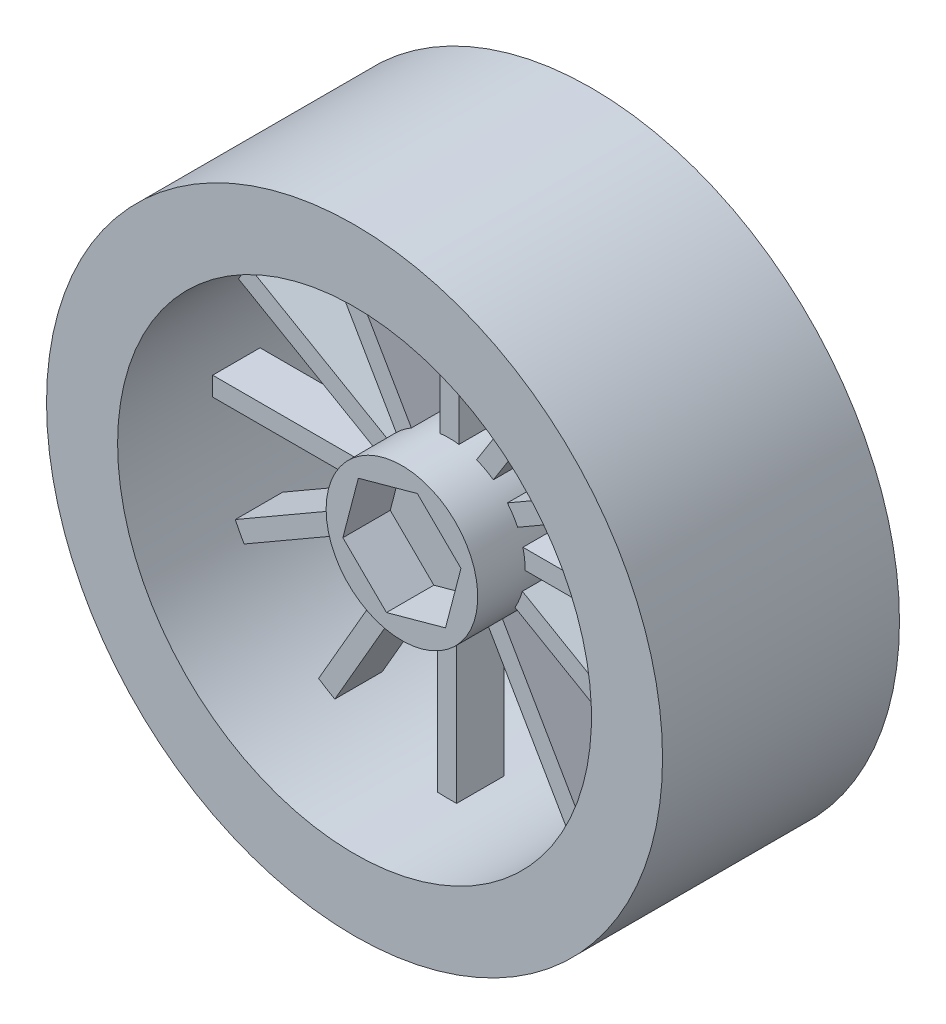
SolidWorks part; units mm, degrees
ref_plane "前视基准面" through (0, 0, 0) normal (0, 0, 1) x (1, 0, 0)
ref_plane "上视基准面" through (0, 0, 0) normal (0, 1, 0) x (1, 0, 0)
ref_plane "右视基准面" through (0, 0, 0) normal (1, 0, 0) x (0, 0, -1)
sketch "草图1" plane through (0, 0, 0) normal (0, 0, 1) x (1, 0, 0)
  circle A0 centre (0, 0) radius 32.5
extrude "凸台-拉伸1" add sketch "草图1" along normal blind 25
sketch "草图2" plane through (0, 0, 0) normal (0, 0, -1) x (-1, 0, 0)
  circle A0 centre (0, 0) radius 25
extrude "切除-拉伸1" cut sketch "草图2" against normal blind 25
sketch "草图6" plane through (0, 0, 0) normal (0, 0, -1) x (-1, 0, 0)
  circle A0 centre (0, 0) radius 8
extrude "凸台-拉伸3" add sketch "草图6" against normal blind 20 separate body contours A0
sketch "草图7" plane through (0, 0, 0) normal (0, 0, -1) x (-1, 0, 0)
  circle A0 centre (0, 0) radius 8
extrude "切除-拉伸2" cut sketch "草图7" against normal blind 5
sketch "草图8" plane through (0, 0, 5) normal (0, 0, -1) x (-1, 0, 0)
  line L1 (6.2049, 0) -> (3.1024, 5.3736)
  line L2 (3.1024, 5.3736) -> (-3.1024, 5.3736)
  line L3 (-3.1024, 5.3736) -> (-6.2049, 0)
  line L4 (-6.2049, 0) -> (-3.1024, -5.3736)
  line L5 (-3.1024, -5.3736) -> (3.1024, -5.3736)
  line L6 (3.1024, -5.3736) -> (6.2049, 0)
  circle A0 centre (0, 0) radius 5.3736 construction
extrude "切除-拉伸3" cut sketch "草图8" against normal blind 5
sketch "草图9" plane through (0, 0, 20) normal (0, 0, 1) x (1, 0, 0)
  line L1 (-1.6308, -6.2524) -> (4.5993, -4.5385)
  line L2 (4.5993, -4.5385) -> (6.2301, 1.7139)
  line L3 (6.2301, 1.7139) -> (1.6308, 6.2524)
  line L4 (1.6308, 6.2524) -> (-4.5993, 4.5385)
  line L5 (-4.5993, 4.5385) -> (-6.2301, -1.7139)
  line L6 (-6.2301, -1.7139) -> (-1.6308, -6.2524)
  circle A0 centre (0, 0) radius 5.5959 construction
extrude "切除-拉伸4" cut sketch "草图9" against normal blind 5
sketch "草图11" plane through (0, -0.7321, 10) normal (0, 0, -1) x (-1, 0, 0)
  line L0 (28.0549, 0) -> (7.0549, 0)
  point P4 (0, 0)
  point P5 (0, 0)
  point P6 (23.5179, -0.2744)
  point P7 (7.0549, 0)
  dimension "D1" = 21
extrude "拉伸-薄壁1" add sketch "草图11" against normal blind 5 thin
sketch "草图15" plane through (0.7839, -0.0874, 10) normal (0, 0, -1) x (-1, 0, 0)
  line L0 (-6.2049, 0) -> (-24.2049, 0)
extrude "拉伸-薄壁8" add sketch "草图15" against normal blind 5 thin
sketch "草图17" plane through (1.0214, 0, 10) normal (0, 0, -1) x (-1, 0, 0)
  line L0 (0, 5.3736) -> (0, 25)
extrude "拉伸-薄壁9" add sketch "草图17" against normal blind 5 thin
sketch "草图19" plane through (0, 0, 10) normal (0, 0, -1) x (-1, 0, 0)
  line L0 (1.2225, 0) -> (1.2225, -25)
extrude "拉伸-薄壁10" add sketch "草图19" against normal blind 5 thin
sketch "草图22" plane through (0.5234, 0, 10) normal (0, 0, -1) x (-1, 0, 0)
  line L0 (0, 0) -> (-13.3698, 21.1246)
extrude "拉伸-薄壁12" add sketch "草图22" against normal blind 5 thin
sketch "草图23" plane through (0, -0.7023, 10) normal (0, 0, -1) x (-1, 0, 0)
  line L0 (0, 0) -> (-22.4096, 12.9382)
extrude "拉伸-薄壁13" add sketch "草图23" against normal blind 5 thin
sketch "草图25" plane through (0, 0.8993, 10) normal (0, 0, -1) x (-1, 0, 0)
  line L0 (0, 0) -> (21.6506, 12.5)
extrude "拉伸-薄壁16" add sketch "草图25" against normal blind 5 thin
sketch "草图26" plane through (0, 0, 10) normal (0, 0, -1) x (-1, 0, 0)
  line L0 (0, 0) -> (13.4916, 23.3682)
extrude "拉伸-薄壁18" add sketch "草图26" against normal blind 5 thin
sketch "草图27" plane through (0, 0, 10) normal (0, 0, -1) x (-1, 0, 0)
  line L0 (0, 0) -> (-23.0674, -13.318)
extrude "拉伸-薄壁20" add sketch "草图27" against normal blind 5 thin
sketch "草图28" plane through (0, 0, 10) normal (0, 0, -1) x (-1, 0, 0)
  line L0 (0, 0) -> (-13.7314, -23.7834)
extrude "拉伸-薄壁21" add sketch "草图28" against normal blind 5 thin
sketch "草图29" plane through (-1.7525, 0, 10) normal (0, 0, -1) x (-1, 0, 0)
  line L0 (0, 0) -> (13.9696, -24.196)
extrude "拉伸-薄壁22" add sketch "草图29" against normal blind 5 thin
sketch "草图30" plane through (0, 0, 15) normal (0, 0, 1) x (1, 0, 0)
  line L0 (0, 0) -> (-22.6524, -13.0784)
extrude "拉伸-薄壁23" add sketch "草图30" against normal blind 5 thin
